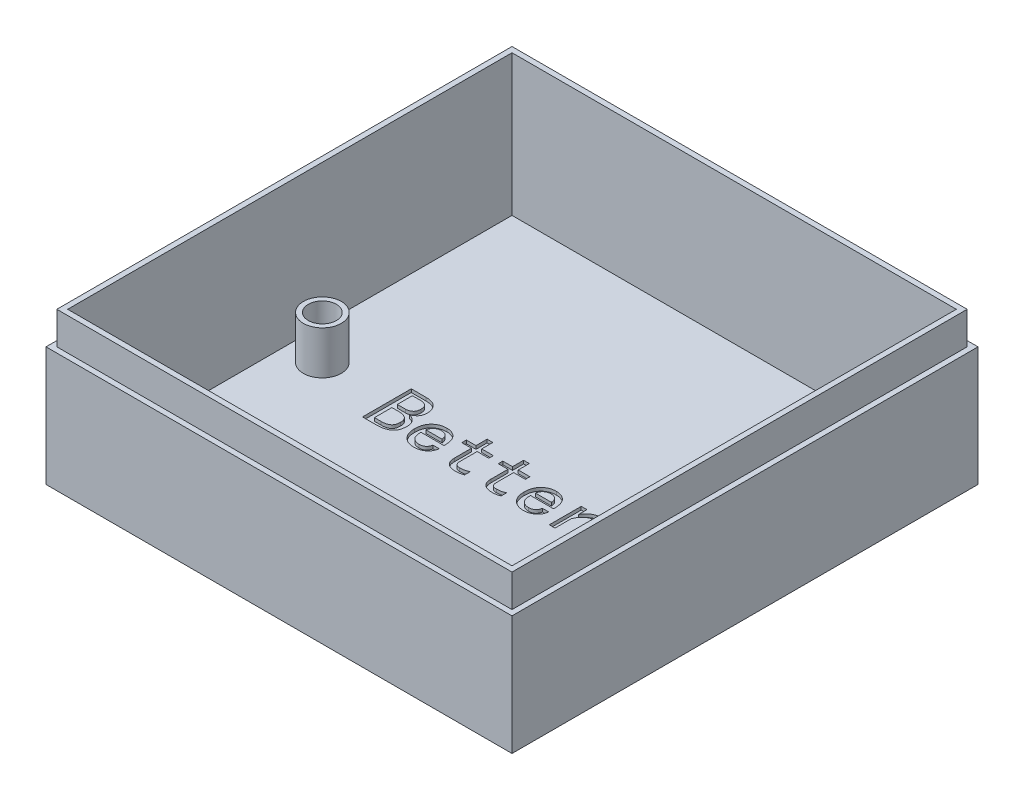
SolidWorks part; units mm, degrees
ref_plane "前视基准面" through (0, 0, 0) normal (0, 0, 1) x (1, 0, 0)
ref_plane "上视基准面" through (0, 0, 0) normal (0, 1, 0) x (1, 0, 0)
ref_plane "右视基准面" through (0, 0, 0) normal (1, 0, 0) x (0, 0, -1)
sketch "草图1" plane through (0, 0, 0) normal (0, 1, 0) x (1, 0, 0)
  line L1 (-27.0091, 17.5714) -> (15.9909, 17.5714)
  line L2 (-27.0091, 17.5714) -> (-27.0091, -25.4286)
  line L3 (-27.0091, -25.4286) -> (15.9909, -25.4286)
  line L4 (15.9909, 17.5714) -> (15.9909, -25.4286)
  dimension "D1" = 43
  dimension "D2" = 43
extrude "凸台-拉伸1" add sketch "草图1" along normal blind 14
sketch "草图2" plane through (0, 14, 0) normal (0, 1, 0) x (1, 0, 0)
  line L0 (-27.0091, -3.9286) -> (15.9909, -3.9286) construction
  line L1 (-26.0091, -24.4286) -> (14.9909, -24.4286)
  line L2 (-26.0091, -24.4286) -> (-26.0091, 16.5714)
  line L3 (-26.0091, 16.5714) -> (14.9909, 16.5714)
  line L4 (14.9909, -24.4286) -> (14.9909, 16.5714)
  line L5 (-26.0091, -24.4286) -> (14.9909, 16.5714) construction
  line L6 (-26.0091, 16.5714) -> (14.9909, -24.4286) construction
  line L7 (-27.0091, 17.5714) -> (-27.0091, -25.4286) construction
  line L8 (15.9909, -25.4286) -> (15.9909, 17.5714) construction
  line L9 (-5.5091, 17.5714) -> (-5.5091, -25.4286) construction
  line L10 (15.9909, 17.5714) -> (-27.0091, 17.5714) construction
  line L11 (-27.0091, -25.4286) -> (15.9909, -25.4286) construction
  point P0 (-5.5091, -3.9286)
  dimension "D1" = 41
  dimension "D2" = 41
extrude "切除-拉伸1" cut sketch "草图2" against normal blind 13
sketch "草图3" plane through (0, 1, 0) normal (0, 1, 0) x (1, 0, 0)
  line L0 (11.9909, -24.4286) -> (11.9909, -20.4286) construction
  line L1 (-26.0091, -24.4286) -> (14.9909, -24.4286) construction
  line L2 (11.9909, -20.4286) -> (14.9909, -20.4286) construction
  line L3 (14.9909, -24.4286) -> (14.9909, 16.5714) construction
  line L4 (11.9909, 16.5714) -> (11.9909, 12.5714) construction
  line L5 (14.9909, 16.5714) -> (-26.0091, 16.5714) construction
  line L6 (11.9909, 12.5714) -> (14.9909, 12.5714) construction
  line L7 (14.9909, -24.4286) -> (14.9909, 16.5714) construction
  line L8 (-26.0091, 16.5714) -> (-26.0091, -24.4286) construction
  line L9 (-26.0091, -3.9286) -> (14.9909, -3.9286) construction
  circle A0 centre (11.9909, -20.4286) radius 1.75
  circle A1 centre (11.9909, 12.5714) radius 1.75
  circle A2 centre (-23.0091, -3.9286) radius 1.75
  dimension "D3" = 3.5
  dimension "D6" = 3.5
  dimension "D7" = 3.5
  dimension "D1" = 3
  dimension "D2" = 4
  dimension "D4" = 3
  dimension "D5" = 4
  dimension "D8" = 3
extrude "凸台-拉伸2" add sketch "草图3" along normal blind 4
sketch "草图4" plane through (0, 5, 0) normal (0, 1, 0) x (1, 0, 0)
  circle A0 centre (-23.0091, -3.9286) radius 1.3
  circle A1 centre (11.9909, 12.5714) radius 1.3
  circle A2 centre (11.9909, -20.4286) radius 1.3
  dimension "D1" = 2.6
  dimension "D2" = 2.6
  dimension "D3" = 2.6
sketch "草图5" plane through (0, 1, 0) normal (0, 1, 0) x (1, 0, 0)
  text T0 "Better++" font "黑体" height 4.5
extrude "切除-拉伸2" cut sketch "草图5" against normal blind 0.3
sketch "草图6" plane through (0, 14, 0) normal (0, 1, 0) x (1, 0, 0)
  line L0 (-26.0091, -3.9286) -> (14.9909, -3.9286) construction
  line L1 (-26.0091, 16.5714) -> (-26.0091, -24.4286) construction
  line L2 (14.9909, -24.4286) -> (14.9909, 16.5714) construction
  line L4 (-27.0091, -25.4286) -> (15.9909, -25.4286)
  line L5 (-27.0091, -25.4286) -> (-27.0091, 17.5714)
  line L6 (-27.0091, 17.5714) -> (15.9909, 17.5714)
  line L7 (15.9909, -25.4286) -> (15.9909, 17.5714)
  line L8 (-27.0091, -25.4286) -> (15.9909, 17.5714) construction
  line L9 (-27.0091, 17.5714) -> (15.9909, -25.4286) construction
  line L10 (-26.5091, -24.9286) -> (15.4909, -24.9286)
  line L11 (-26.5091, -24.9286) -> (-26.5091, 17.0714)
  line L12 (-26.5091, 17.0714) -> (15.4909, 17.0714)
  line L13 (15.4909, -24.9286) -> (15.4909, 17.0714)
  line L14 (-26.5091, -24.9286) -> (15.4909, 17.0714) construction
  line L15 (-26.5091, 17.0714) -> (15.4909, -24.9286) construction
  point P6 (-5.5091, -3.9286)
  point P11 (-5.5091, -3.9286)
  dimension "D1" = 43
  dimension "D2" = 43
  dimension "D3" = 42
  dimension "D4" = 42
extrude "切除-拉伸3" cut sketch "草图6" against normal blind 3
extrude "切除-拉伸4" cut sketch "草图4" against normal through all
sketch "草图9" plane through (0, 0, 0) normal (0, -1, 0) x (1, 0, 0)
  line L0 (-27.0091, 3.9286) -> (15.9909, 3.9286) construction
  line L1 (-27.0091, -17.5714) -> (-27.0091, 25.4286) construction
  line L2 (15.9909, 25.4286) -> (15.9909, -17.5714) construction
  line L3 (-26.0091, -16.5714) -> (-26.0091, 24.4286) construction
  line L4 (11.9909, -12.5714) -> (11.9909, 20.4286)
  circle A0 centre (-23.0091, 3.9286) radius 1.55
  circle A1 centre (11.9909, -12.5714) radius 1.55
  circle A2 centre (11.9909, 20.4286) radius 1.55
  dimension "D2" = 3.1
  dimension "D3" = 3.1
  dimension "D4" = 3.1
  dimension "D1" = 3
extrude "切除-拉伸5" cut sketch "草图9" against normal blind 3 contours A0 | A1 | A2
